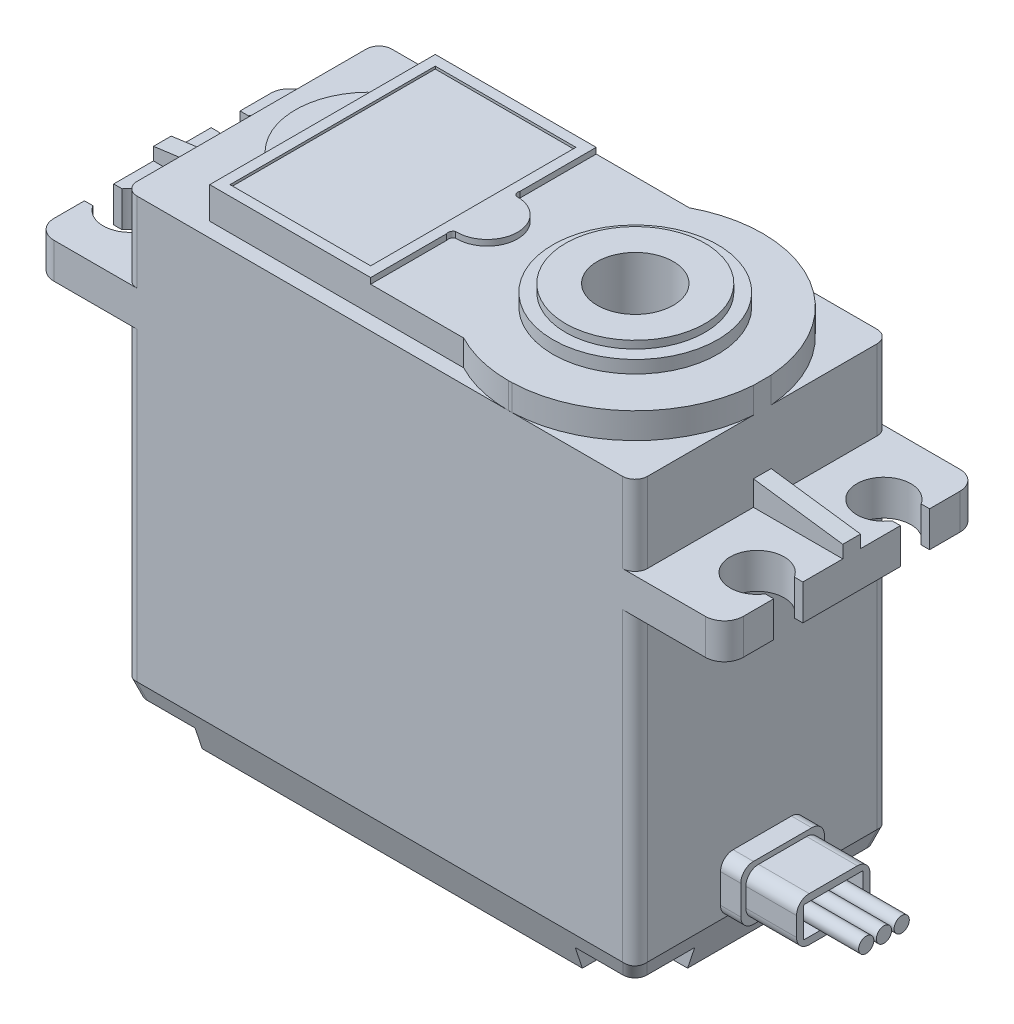
SolidWorks part; units mm, degrees
ref_plane "Ön Düzlem" through (0, 0, 0) normal (0, 0, 1) x (1, 0, 0)
ref_plane "Üst Düzlem" through (0, 0, 0) normal (0, 1, 0) x (1, 0, 0)
ref_plane "Sağ Düzlem" through (0, 0, 0) normal (1, 0, 0) x (0, 0, -1)
sketch "Çizim1" plane through (0, 0, 0) normal (0, 0, 1) x (1, 0, 0)
  line L0 (-48.7593, -35.6983) -> (-8.4593, -35.6983)
  line L1 (-8.4593, -35.6983) -> (-8.4593, -8.5983)
  line L2 (-8.4593, -8.5983) -> (-1.4093, -8.5983)
  line L3 (-1.4093, -8.5983) -> (-1.4093, -5.7983)
  line L4 (-1.4093, -5.7983) -> (-8.4593, -5.7983)
  line L5 (-8.4593, -5.7983) -> (-8.4593, 3.0017)
  line L6 (-8.4593, 3.0017) -> (-48.7593, 3.0017)
  line L7 (-28.6093, 3.0017) -> (-28.6093, -35.6983) construction
  line L8 (-48.7593, -35.6983) -> (-48.7593, -8.5983)
  line L9 (-48.7593, -8.5983) -> (-55.8093, -8.5983)
  line L10 (-55.8093, -8.5983) -> (-55.8093, -5.7983)
  line L11 (-55.8093, -5.7983) -> (-48.7593, -5.7983)
  line L12 (-48.7593, -5.7983) -> (-48.7593, 3.0017)
extrude "Yükseklik-Ekstrüzyon1" add sketch "Çizim1" along normal blind 20.1
ref_plane "Düzlem1" through (0, 0, 10.05) normal (0, 0, 1) x (1, 0, 0)
sketch "Çizim3" plane through (0, 0, 10.05) normal (0, 0, 1) x (1, 0, 0)
  line L0 (-55.8093, -5.7983) -> (-48.7593, -5.7983)
  line L1 (-48.7593, -5.7983) -> (-48.7593, -3.8483)
  line L2 (-48.7593, 3.0017) -> (-48.7593, -5.7983) construction
  line L4 (-55.8093, -5.7983) -> (-55.8093, -4.7983)
  line L5 (-55.8093, -4.7983) -> (-48.7593, -3.8483)
  line L6 (-8.4593, -5.7983) -> (-1.4093, -5.7983)
  line L7 (-1.4093, -5.7983) -> (-1.4093, -4.7983)
  line L8 (-8.4593, -5.7983) -> (-8.4593, -3.8483)
  line L9 (-8.4593, -5.7983) -> (-8.4593, 3.0017) construction
  line L10 (-8.4593, -3.8483) -> (-1.4093, -4.7983)
extrude "Yükseklik-Ekstrüzyon2" add sketch "Çizim3" along normal blind 0.7 and the other way blind 0.7
sketch "Çizim4" plane through (0, 3.0017, 0) normal (0, 1, 0) x (1, 0, 0)
  line L0 (-55.8093, -16.2) -> (-55.1463, -16.2)
  line L1 (-55.8093, -20.1) -> (-55.8093, -10.75) construction
  line L2 (-48.7593, -20.1) -> (-55.8093, -20.1) construction
  line L3 (-55.8093, -16.2) -> (-55.8093, -13.8927)
  line L4 (-55.8093, -13.8927) -> (-55.1463, -13.8927)
  line L5 (-55.8093, -15.0464) -> (-53.3593, -15.0464) construction
  line L11 (-55.8093, -3.9163) -> (-55.1463, -3.9163)
  line L12 (-55.8093, -3.9163) -> (-55.8093, -6.2)
  line L13 (-55.8093, -6.2) -> (-55.1463, -6.2)
  line L14 (-1.4093, -6.2) -> (-2.0723, -6.2)
  line L15 (-1.4093, -3.9) -> (-1.4093, -6.2)
  line L16 (-1.4093, -3.9) -> (-2.0723, -3.9)
  line L17 (-1.4093, -13.9022) -> (-2.0723, -13.9022)
  line L18 (-1.4093, -16.2) -> (-1.4093, -13.9022)
  line L19 (-1.4093, -16.2) -> (-2.0723, -16.2)
  arc A6 (-2.0723, -3.9) -> (-2.0723, -6.2) centre (-3.8652, -5.05) ccw
  arc A7 (-2.0723, -13.9022) -> (-2.0723, -16.2) centre (-3.8659, -15.0511) ccw
  arc A8 (-55.1463, -13.8927) -> (-55.1463, -16.2) centre (-53.3557, -15.0464) cw
  arc A9 (-55.1463, -3.9163) -> (-55.1463, -6.2) centre (-53.3482, -5.0582) cw
  dimension "D1" = 3.9
  dimension "D3" = 2.3
  dimension "D4" = 0.663
  dimension "D5" = 0.663
extrude "Kes-Ekstrüzyon2" cut sketch "Çizim4" against normal blind 50
fillet "Radyus1" radius 1.5 4 edges at (-1.4093, -7.1983, 0) (-1.4093, -7.1983, 20.1) (-55.8093, -7.1983, 20.1) (-55.8093, -7.1983, 0)
fillet "Radyus2" radius 1 8 edges at (-8.4593, -22.1483, 0) (-8.4593, -1.3983, 0) (-48.7593, -22.1483, 0) (-48.7593, -1.3983, 0) (-8.4593, -22.1483, 20.1) (-8.4593, -1.3983, 20.1) (-48.7593, -22.1483, 20.1) (-48.7593, -1.3983, 20.1)
sketch "Çizim5" plane through (0, 3.0017, 0) normal (0, 1, 0) x (1, 0, 0)
  line L0 (-8.4593, -19.1) -> (-8.4593, -1) construction
  line L1 (-18.4593, 0) -> (-48.7603, 0)
  line L2 (-9.4593, 0) -> (-47.7593, 0) construction
  line L3 (-47.7593, 0) -> (-54.3093, 0) construction
  line L4 (-48.7603, 0) -> (-48.7603, -20.1)
  line L5 (-47.7593, -20.1) -> (-54.3093, -20.1) construction
  line L6 (-48.7603, -20.1) -> (-18.4593, -20.1)
  line L7 (-9.4593, -20.1) -> (-47.7593, -20.1) construction
  line L8 (-43.1703, -1.15) -> (-23.1275, -1.15)
  line L9 (-43.1703, -1.15) -> (-43.1703, -5.56)
  line L10 (-18.4593, 0) -> (-1.4093, 0)
  line L11 (-43.1703, -18.95) -> (-23.1275, -18.95)
  line L12 (-43.1703, -18.95) -> (-43.1703, -14.54)
  line L13 (-1.4093, 0) -> (-1.4093, -20.1)
  line L14 (-1.4093, -20.1) -> (-18.4593, -20.1)
  arc A0 (-23.1275, -18.95) -> (-18.4593, -20.1) centre (-18.4593, -10.05) ccw
  arc A1 (-43.1703, -5.56) -> (-43.1703, -14.54) centre (-39.5158, -10.05) ccw
  arc A2 (-18.4593, 0) -> (-23.1275, -1.15) centre (-18.4593, -10.05) ccw
  arc A3 (-18.4593, 0) -> (-18.4593, -20.1) centre (-18.4593, -10.05) cw
  point P0 (-18.4593, -10.05)
  line M14 (-9.4593, 0) -> (-47.7593, 0)
  arc M15 (-47.7593, 0) -> (-48.7593, -1) centre (-47.7593, -1) ccw
  line M16 (-48.7593, -1) -> (-48.7593, -19.1)
  arc M17 (-48.7593, -19.1) -> (-47.7593, -20.1) centre (-47.7593, -19.1) ccw
  line M18 (-47.7593, -20.1) -> (-9.4593, -20.1)
  dimension "D3" = 5.7893
  dimension "D1" = 10
  dimension "D2" = 5.59
  dimension "D4" = 1.15
extrude "Kes-Ekstrüzyon4" cut sketch "Çizim5" against normal blind 2.5 contours A2 A0 L11 L12 A1 L9 L8 M14 M15 M16 M17 M18
sketch "Çizim7" plane through (0, 3.0017, 0) normal (0, 1, 0) x (1, 0, 0)
  line L0 (-43.1703, -5.56) -> (-43.1703, -14.54)
  line L1 (-43.1703, -18.95) -> (-43.1703, -14.54) construction
  arc A0 (-43.1703, -5.56) -> (-43.1703, -14.54) centre (-39.5158, -10.05) ccw construction
  arc A2 (-43.1703, -5.56) -> (-43.1703, -14.54) centre (-39.5158, -10.05) ccw
extrude "Kes-Ekstrüzyon6" cut sketch "Çizim7" against normal blind 0.4
sketch "Çizim8" plane through (0, 3.0017, 0) normal (0, 1, 0) x (1, 0, 0)
  line L0 (-30.4703, -1.15) -> (-23.1275, -1.15)
  line L1 (-30.4703, -1.15) -> (-30.4703, -7.155)
  line L2 (-43.1703, -1.15) -> (-23.1275, -1.15) construction
  line L3 (-43.1703, -1.15) -> (-43.1703, -18.95) construction
  line L4 (-30.4703, -18.95) -> (-30.4703, -12.945)
  line L5 (-30.4703, -18.95) -> (-23.1275, -18.95)
  arc A0 (-30.2662, -12.4481) -> (-30.2662, -7.6519) centre (-30.1703, -10.05) ccw
  arc A1 (-30.4703, -7.155) -> (-30.2662, -7.6519) centre (-30.1198, -7.3014) ccw
  arc A2 (-30.4703, -12.945) -> (-30.2662, -12.4481) centre (-30.1198, -12.7986) cw
  arc A5 (-23.1275, -18.95) -> (-23.1275, -1.15) centre (-18.4593, -10.05) ccw
  point P18 (-23.1275, -1.15)
  point P19 (-23.1275, -18.95)
  dimension "D1" = 12.7
  dimension "D3" = 0.3
extrude "Kes-Ekstrüzyon7" cut sketch "Çizim8" against normal blind 0.46
sketch "Çizim9" plane through (0, 3.0017, 0) normal (0, 1, 0) x (1, 0, 0)
  line L0 (-18.4593, 0) -> (-8.4593, 0)
  line L1 (-2.9093, 0) -> (-9.4593, 0) construction
  line L2 (-8.4593, 0) -> (-8.4593, -9.35)
  line L4 (-8.4593, -20.0999) -> (-8.4593, -10.7499)
  line L5 (-18.4593, -20.0999) -> (-8.4593, -20.0999)
  arc A0 (-18.4593, 0) -> (-8.4593, -9.35) centre (-18.4849, -10.05) cw
  arc A1 (-18.4593, -20.0999) -> (-8.4593, -10.7499) centre (-18.4849, -10.05) ccw
extrude "Kes-Ekstrüzyon8" cut sketch "Çizim9" against normal blind 2.5
sketch "Çizim10" plane through (0, 0, 20.1) normal (0, 0, 1) x (1, 0, 0)
  line L0 (-9.4593, -5.7983) -> (-9.4593, 3.0017) construction
  line L1 (-18.4593, 3.0017) -> (-9.4593, 3.0017)
  line L2 (-18.4593, 3.0017) -> (-18.4593, 0.5017)
  line L3 (-18.4593, 0.5017) -> (-9.4593, 0.5017)
  line L4 (-9.4593, 3.0017) -> (-9.4593, 0.5017)
  line L5 (-8.4593, 0.5017) -> (-18.4593, 0.5017) construction
extrude "Kes-Ekstrüzyon9" cut sketch "Çizim10" against normal blind 0.005
sketch "Çizim11" plane through (0, 3.0017, 0) normal (0, 1, 0) x (1, 0, 0)
  line L0 (-43.1703, -1.15) -> (-43.1703, -5.56) construction
  line L1 (-42.3703, -1.95) -> (-31.2703, -1.95)
  line L2 (-42.3703, -1.95) -> (-42.3703, -18.15)
  line L3 (-42.3703, -18.15) -> (-31.2703, -18.15)
  line L4 (-31.2703, -1.95) -> (-31.2703, -18.15)
  line L5 (-43.1703, -18.95) -> (-23.1275, -18.95) construction
  line L6 (-43.1703, -1.15) -> (-23.1275, -1.15) construction
  line L7 (-30.4703, -1.15) -> (-30.4703, -7.155) construction
  point P6 (-43.1703, -3.355)
  dimension "D1" = 0.8
  dimension "D2" = 0.8
  dimension "D3" = 0.8
  dimension "D4" = 0.8
extrude "Kes-Ekstrüzyon10" cut sketch "Çizim11" against normal blind 0.2
sketch "Çizim12" plane through (0, 2.5417, 0) normal (0, 1, 0) x (1, 0, 0)
  circle A0 centre (-18.4849, -10.05) radius 5.5
  circle A1 centre (-18.4849, -10.05) radius 6.5
extrude "Yükseklik-Ekstrüzyon3" add sketch "Çizim12" along normal blind 1
sketch "Çizim13" plane through (0, 2.5417, 0) normal (0, 1, 0) x (1, 0, 0)
  circle A0 centre (-18.4849, -10.05) radius 5.5
extrude "Yükseklik-Ekstrüzyon4" add sketch "Çizim13" along normal blind 1.6
sketch "Çizim14" plane through (0, 4.1417, 0) normal (0, 1, 0) x (1, 0, 0)
  circle A0 centre (-18.4849, -10.05) radius 3
extrude "Kes-Ekstrüzyon11" cut sketch "Çizim14" against normal blind 10
sketch "Çizim15" plane through (-48.7593, 0, 0) normal (-1, 0, 0) x (0, 0, 1)
  line L0 (20.1, -35.6983) -> (20.1, -32.6983)
  line L1 (20.1, -8.5983) -> (20.1, -35.6983) construction
  line L2 (20.1, -35.6983) -> (19.1, -35.6983)
  line L3 (19.1, -35.6983) -> (1, -35.6983) construction
  line L4 (19.1, -35.6983) -> (20.1, -35.6983) construction
  line L5 (19.1, -35.6983) -> (20.1, -32.6983)
  line L6 (10.05, -28.8885) -> (10.05, 28.8885) construction
  line L7 (0, -35.6983) -> (1, -35.6983)
  line L8 (1, -35.6983) -> (0, -32.6983)
  line L9 (0, -35.6983) -> (0, -32.6983)
extrude "Kes-Ekstrüzyon12" cut sketch "Çizim15" against normal blind 50
sketch "Çizim17" plane through (0, 0, 20.1) normal (0, 0, 1) x (1, 0, 0)
  line L0 (-48.7593, -32.6983) -> (-48.7593, -35.6983)
  line L1 (-48.7593, -35.6983) -> (-48.7593, -8.5983) construction
  line L2 (-48.7593, -35.6983) -> (-47.7593, -35.6983)
  line L3 (-8.4593, -35.6983) -> (-48.7593, -35.6983) construction
  line L4 (-47.7593, -35.6983) -> (-48.7593, -32.6983)
  line L5 (-28.6093, -35.6983) -> (-28.6093, -29.863) construction
  line L6 (-8.4593, -35.6983) -> (-9.4593, -35.6983)
  line L7 (-8.4593, -32.6983) -> (-8.4593, -35.6983)
  line L8 (-9.4593, -35.6983) -> (-8.4593, -32.6983)
extrude "Kes-Ekstrüzyon13" cut sketch "Çizim17" against normal blind 50
fillet "Radyus3" radius 1 4 edges at (-9.1057, -34.6377, 0.6464) (-48.1128, -34.6377, 0.6464) (-9.1057, -34.6377, 19.4536) (-48.1128, -34.6377, 19.4536)
sketch "Çizim18" plane through (0, -35.6983, 0) normal (0, -1, 0) x (1, 0, 0)
  line L0 (-48.7593, 20.1) -> (-43.6093, 20.1)
  line L1 (-54.3093, 20.1) -> (-47.7593, 20.1) construction
  line L2 (-9.4593, 20.1) -> (-47.7593, 20.1) construction
  line L3 (-48.7593, 20.1) -> (-48.7593, 14.95)
  line L4 (-48.7593, 1) -> (-48.7593, 19.1) construction
  line L5 (-48.7593, 14.95) -> (-46.2593, 14.95)
  line L6 (-43.6093, 20.1) -> (-43.6093, 17.6)
  line L7 (-28.6093, 20.1) -> (-28.6093, 9.0698) construction
  line L8 (-48.7593, 10.05) -> (-27.3387, 10.05) construction
  line L9 (-48.7593, 19.1) -> (-48.7593, 1) construction
  line L10 (-48.7593, 5.15) -> (-46.2593, 5.15)
  line L11 (-48.7593, 0) -> (-48.7593, 5.15)
  line L12 (-48.7593, 0) -> (-43.6093, 0)
  line L13 (-43.6093, 0) -> (-43.6093, 2.5)
  line L14 (-8.4593, 14.95) -> (-10.9593, 14.95)
  line L15 (-13.6093, 20.1) -> (-13.6093, 17.6)
  line L16 (-8.4593, 20.1) -> (-8.4593, 14.95)
  line L17 (-8.4593, 20.1) -> (-13.6093, 20.1)
  line L18 (-8.4593, 0) -> (-13.6093, 0)
  line L19 (-13.6093, 0) -> (-13.6093, 2.5)
  line L20 (-8.4593, 0) -> (-8.4593, 5.15)
  line L21 (-8.4593, 5.15) -> (-10.9593, 5.15)
  arc A0 (-43.6093, 17.6) -> (-46.2593, 14.95) centre (-46.2593, 17.6) cw
  arc A1 (-43.6093, 2.5) -> (-46.2593, 5.15) centre (-46.2593, 2.5) ccw
  arc A2 (-13.6093, 17.6) -> (-10.9593, 14.95) centre (-10.9593, 17.6) ccw
  arc A3 (-13.6093, 2.5) -> (-10.9593, 5.15) centre (-10.9593, 2.5) cw
extrude "Kes-Ekstrüzyon14" cut sketch "Çizim18" against normal blind 1.7
sketch "Çizim19" plane through (0, -33.9983, 0) normal (0, -1, 0) x (-1, 0, 0)
  point P0 (46.2593, -17.6)
sketch "Çizim20" plane through (0, -33.9983, 0) normal (0, -1, 0) x (-1, 0, 0)
  line L0 (47.7593, -10.05) -> (44.2993, -10.05) construction
  line L1 (47.7593, -5.15) -> (47.7593, -14.95) construction
  line L2 (28.6093, -19.1) -> (28.6093, -16.25) construction
  line L3 (13.6093, -19.1) -> (43.6093, -19.1) construction
  circle A0 centre (46.2593, -17.6) radius 1.35
  circle A1 centre (46.2593, -16.25) radius 0.1097
  circle A2 centre (10.9593, -17.6) radius 1.35
  circle A3 centre (46.2593, -2.5) radius 1.35
  circle A4 centre (10.9593, -2.5) radius 1.35
  point P19 (0, 0)
  dimension "D1" = 2.7
extrude "Kes-Ekstrüzyon15" cut sketch "Çizim20" against normal blind 32 contours A3 | A2 | A4 | A0
sketch "Çizim21" plane through (-8.4593, 0, 0) normal (1, 0, 0) x (0, 0, -1)
  line L0 (-1, -32.6983) -> (-19.1, -32.6983) construction
  line L1 (-13.35, -32.6983) -> (-6.75, -32.6983)
  line L2 (-13.35, -32.6983) -> (-13.35, -28.3983)
  line L3 (-13.35, -28.3983) -> (-6.75, -28.3983)
  line L4 (-6.75, -32.6983) -> (-6.75, -28.3983)
  line L5 (-10.05, 28.8885) -> (-10.05, -28.8885) construction
  dimension "D1" = 6.6
  dimension "D2" = 4.3
  dimension "D3" = 3.3
extrude "Yükseklik-Ekstrüzyon5" add sketch "Çizim21" along normal blind 1.6
fillet "Radyus4" radius 1 4 edges at (-7.6593, -28.3983, 13.35) (-7.6593, -28.3983, 6.75) (-7.6593, -32.6983, 6.75) (-7.6593, -32.6983, 13.35)
sketch "Çizim22" plane through (-6.8593, 0, 0) normal (1, 0, 0) x (0, 0, -1)
  line L0 (-7.75, -28.3983) -> (-12.35, -28.3983) construction
  line L1 (-12.95, -28.7983) -> (-7.15, -28.7983)
  line L2 (-12.95, -28.7983) -> (-12.95, -32.2983)
  line L3 (-12.95, -32.2983) -> (-7.15, -32.2983)
  line L4 (-7.15, -28.7983) -> (-7.15, -32.2983)
  line L5 (-6.75, -31.6983) -> (-6.75, -29.3983) construction
  line L6 (-12.35, -32.6983) -> (-7.75, -32.6983) construction
  line L7 (-13.35, -29.3983) -> (-13.35, -31.6983) construction
  dimension "D1" = 0.4
  dimension "D2" = 0.4
  dimension "D3" = 0.4
  dimension "D4" = 0.4
extrude "Yükseklik-Ekstrüzyon6" add sketch "Çizim22" along normal blind 4
fillet "Radyus6" radius 1 4 edges at (-4.8593, -28.7983, 7.15) (-4.8593, -32.2983, 7.15) (-4.8593, -32.2983, 12.95) (-4.8593, -28.7983, 12.95)
sketch "Çizim23" plane through (-2.8593, 0, 0) normal (1, 0, 0) x (0, 0, -1)
  line L0 (-8.15, -28.7983) -> (-11.95, -28.7983) construction
  line L1 (-12.4, -29.3483) -> (-7.7, -29.3483)
  line L2 (-12.4, -29.3483) -> (-12.4, -31.7483)
  line L3 (-12.4, -31.7483) -> (-7.7, -31.7483)
  line L4 (-7.7, -29.3483) -> (-7.7, -31.7483)
  line L5 (-7.15, -31.2983) -> (-7.15, -29.7983) construction
  line L6 (-12.95, -29.7983) -> (-12.95, -31.2983) construction
  line L7 (-11.95, -32.2983) -> (-8.15, -32.2983) construction
  dimension "D1" = 0.55
  dimension "D2" = 0.55
  dimension "D3" = 0.55
  dimension "D4" = 0.55
extrude "Kes-Ekstrüzyon17" cut sketch "Çizim23" against normal up to surface (4 mm away) up to face at (-6.8593, -30.5483, 10.05)
fillet "Radyus7" radius 0.1 4 edges at (-4.8593, -31.7483, 12.4) (-4.8593, -31.7483, 7.7) (-4.8593, -29.3483, 7.7) (-4.8593, -29.3483, 12.4)
sketch "Çizim24" plane through (-6.8593, 0, 0) normal (1, 0, 0) x (0, 0, -1)
  line L0 (-12.4, -29.4483) -> (-12.4, -31.6483) construction
  circle A0 centre (-11.45, -30.5483) radius 0.6
  circle A1 centre (-10.05, -30.5483) radius 0.6
  circle A2 centre (-8.65, -30.5483) radius 0.6
  dimension "D1" = 1.2
  dimension "D2" = 1.2
  dimension "D3" = 1.2
  dimension "D4" = 1.4
  dimension "D5" = 1.4
  dimension "D6" = 0.95
extrude "Yükseklik-Ekstrüzyon7" add sketch "Çizim24" along normal blind 8
